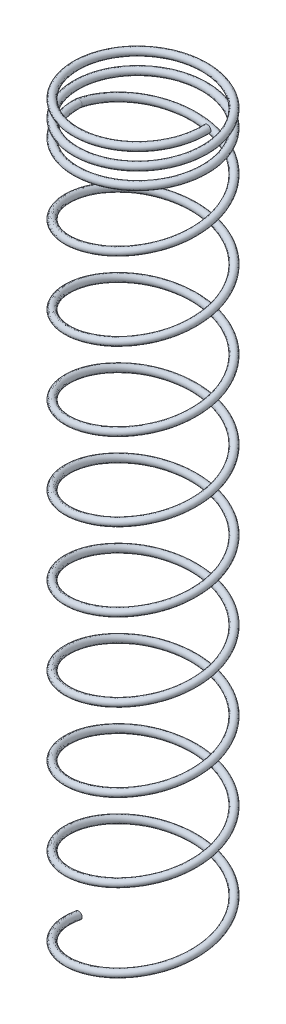
SolidWorks part; units mm, degrees
material "Alloy Steel"
ref_plane "Front Plane" through (0, 0, 0) normal (0, 0, 1) x (1, 0, 0)
ref_plane "Top Plane" through (0, 0, 0) normal (0, 1, 0) x (1, 0, 0)
ref_plane "Right Plane" through (0, 0, 0) normal (1, 0, 0) x (0, 0, -1)
other "Configuration Table"
sketch "Sketch1" plane through (0, 0, 0) normal (0, 1, 0) x (1, 0, 0)
  circle A0 centre (0, 0) radius 2.5019
  dimension "D1" = 5.0038
curve "Helix/Spiral1" pitch 2.7771 height 24.9936 turns 9
sketch "Sketch2" plane through (0, 0, 0) normal (0, 0, 1) x (1, 0, 0)
  circle A0 centre (-2.2872, 0.1845) radius 0.127
  spline S1 degree 3 poles (-2.5019, 0) (-2.5019, 0.0575) (-2.3716, 0.1737) (-1.8152, 0.3471) (-0.9824, 0.5207) (0, 0.6943) (0.9824, 0.8678) (1.8152, 1.0414) (2.3716, 1.215) (2.567, 1.3885) (2.3716, 1.5621) (1.8152, 1.7357) (0.7048, 1.9671) (-0.7048, 2.1985) (-1.8152, 2.4299) (-2.3716, 2.6035) (-2.567, 2.7771) (-2.3716, 2.9506) (-1.8152, 3.1242) (-0.7048, 3.3556) (0.7048, 3.587) (1.8152, 3.8185) (2.3716, 3.992) (2.567, 4.1656) (2.3716, 4.3392) (1.8152, 4.5127) (0.7048, 4.7442) (-0.7048, 4.9756) (-1.8152, 5.207) (-2.3716, 5.3806) (-2.567, 5.5541) (-2.3716, 5.7277) (-1.8152, 5.9013) (-0.7048, 6.1327) (0.7048, 6.3641) (1.8152, 6.5955) (2.3716, 6.7691) (2.567, 6.9427) (2.3716, 7.1162) (1.8152, 7.2898) (0.7048, 7.5212) (-0.7048, 7.7526) (-1.8152, 7.9841) (-2.3716, 8.1576) (-2.567, 8.3312) (-2.3716, 8.5048) (-1.8152, 8.6783) (-0.7048, 8.9098) (0.7048, 9.1412) (1.8152, 9.3726) (2.3716, 9.5462) (2.567, 9.7197) (2.3716, 9.8933) (1.8152, 10.0669) (0.7048, 10.2983) (-0.7048, 10.5297) (-1.8152, 10.7611) (-2.3716, 10.9347) (-2.567, 11.1083) (-2.3716, 11.2818) (-1.8152, 11.4554) (-0.7048, 11.6868) (0.7048, 11.9182) (1.8152, 12.1497) (2.3716, 12.3232) (2.567, 12.4968) (2.3716, 12.6704) (1.8152, 12.8439) (0.7048, 13.0754) (-0.7048, 13.3068) (-1.8152, 13.5382) (-2.3716, 13.7118) (-2.567, 13.8853) (-2.3716, 14.0589) (-1.8152, 14.2325) (-0.7048, 14.4639) (0.7048, 14.6953) (1.8152, 14.9267) (2.3716, 15.1003) (2.567, 15.2739) (2.3716, 15.4474) (1.8152, 15.621) (0.7048, 15.8524) (-0.7048, 16.0838) (-1.8152, 16.3153) (-2.3716, 16.4888) (-2.567, 16.6624) (-2.3716, 16.836) (-1.8152, 17.0095) (-0.7048, 17.241) (0.7048, 17.4724) (1.8152, 17.7038) (2.3716, 17.8774) (2.567, 18.0509) (2.3716, 18.2245) (1.8152, 18.3981) (0.7048, 18.6295) (-0.7048, 18.8609) (-1.8152, 19.0923) (-2.3716, 19.2659) (-2.567, 19.4395) (-2.3716, 19.613) (-1.8152, 19.7866) (-0.7048, 20.018) (0.7048, 20.2494) (1.8152, 20.4809) (2.3716, 20.6544) (2.567, 20.828) (2.3716, 21.0016) (1.8152, 21.1751) (0.7048, 21.4066) (-0.7048, 21.638) (-1.8152, 21.8694) (-2.3716, 22.043) (-2.567, 22.2165) (-2.3716, 22.3901) (-1.8152, 22.5637) (-0.7048, 22.7951) (0.7048, 23.0265) (1.8152, 23.2579) (2.3716, 23.4315) (2.567, 23.6051) (2.3716, 23.7786) (1.8152, 23.9522) (0.9824, 24.1258) (0, 24.2993) (-0.9824, 24.4729) (-1.8152, 24.6465) (-2.3716, 24.8199) (-2.5019, 24.9361) (-2.5019, 24.9936) knots 0 0 0 0 0.006944 0.013889 0.020833 0.027778 0.034722 0.041667 0.048611 0.055556 0.0625 0.069444 0.076389 0.090278 0.097222 0.104167 0.111111 0.118056 0.125 0.131944 0.145833 0.152778 0.159722 0.166667 0.173611 0.180556 0.1875 0.201389 0.208333 0.215278 0.222222 0.229167 0.236111 0.243056 0.256944 0.263889 0.270833 0.277778 0.284722 0.291667 0.298611 0.3125 0.319444 0.326389 0.333333 0.340278 0.347222 0.354167 0.368056 0.375 0.381944 0.388889 0.395833 0.402778 0.409722 0.423611 0.430556 0.4375 0.444444 0.451389 0.458333 0.465278 0.479167 0.486111 0.493056 0.5 0.506944 0.513889 0.520833 0.534722 0.541667 0.548611 0.555556 0.5625 0.569444 0.576389 0.590278 0.597222 0.604167 0.611111 0.618056 0.625 0.631944 0.645833 0.652778 0.659722 0.666667 0.673611 0.680556 0.6875 0.701389 0.708333 0.715278 0.722222 0.729167 0.736111 0.743056 0.756944 0.763889 0.770833 0.777778 0.784722 0.791667 0.798611 0.8125 0.819444 0.826389 0.833333 0.840278 0.847222 0.854167 0.868056 0.875 0.881944 0.888889 0.895833 0.902778 0.909722 0.923611 0.930556 0.9375 0.944444 0.951389 0.958333 0.965278 0.972222 0.979167 0.986111 0.993056 1 1 1 1 construction
  dimension "D1" = 0.254
  dimension "D2" = 2.2946
sweep "Sweep1" add profiles "Sketch2" path "Helix/Spiral1"
ref_plane "Plane1" through (0, 24.9276, 0) normal (0, 1, 0) x (1, 0, 0)
sketch "Sketch4" plane through (0, 24.9276, 0) normal (0, 1, 0) x (1, 0, 0)
  circle A0 centre (0, 0) radius 2.5019
  dimension "D1" = 5.0038
curve "Helix/Spiral2" pitch 0.6005 height 1.5011 turns 2.5
sketch "Sketch5" plane through (0, 0, 0) normal (0, 0, 1) x (1, 0, 0)
  circle A0 centre (-2.2872, 25.1781) radius 0.127
  dimension "D1" = 0.254
  dimension "D2" = 25.1781
  dimension "D3" = 2.2872
sweep "Sweep2" add profiles "Sketch5" path "Helix/Spiral2"
